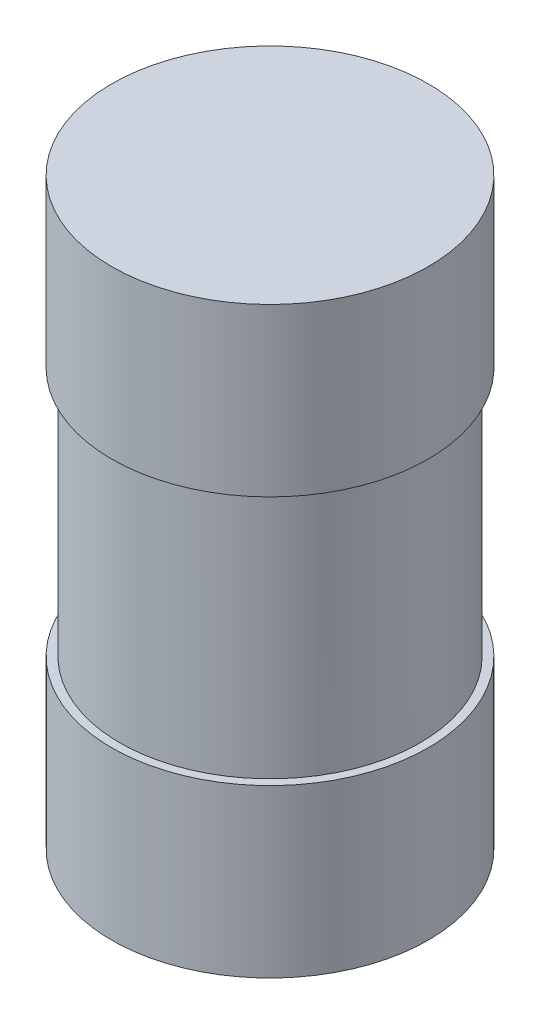
SolidWorks part; units mm, degrees
material "18350"
ref_plane "Front Plane" through (0, 0, 0) normal (0, 0, 1) x (1, 0, 0)
ref_plane "Top Plane" through (0, 0, 0) normal (0, 1, 0) x (1, 0, 0)
ref_plane "Right Plane" through (0, 0, 0) normal (1, 0, 0) x (0, 0, -1)
sketch "Sketch1" plane through (0, 0, 0) normal (0, 1, 0) x (1, 0, 0)
  circle A0 centre (0, 0) radius 9
  dimension "D1" = 18
extrude "Boss-Extrude1" add sketch "Sketch1" along normal blind 35
sketch "Sketch2" plane through (0, 35, 0) normal (0, 1, 0) x (1, 0, 0)
  circle A0 centre (0, 0) radius 9
  circle A1 centre (0, 0) radius 9.5
  dimension "D1" = 0.5
extrude "Boss-Extrude2" add sketch "Sketch2" against normal blind 10
sketch "Sketch3" plane through (0, 0, 0) normal (0, -1, 0) x (-1, 0, 0)
  circle A0 centre (0, 0) radius 9
  circle A1 centre (0, 0) radius 9.5
extrude "Boss-Extrude3" add sketch "Sketch3" against normal blind 10
